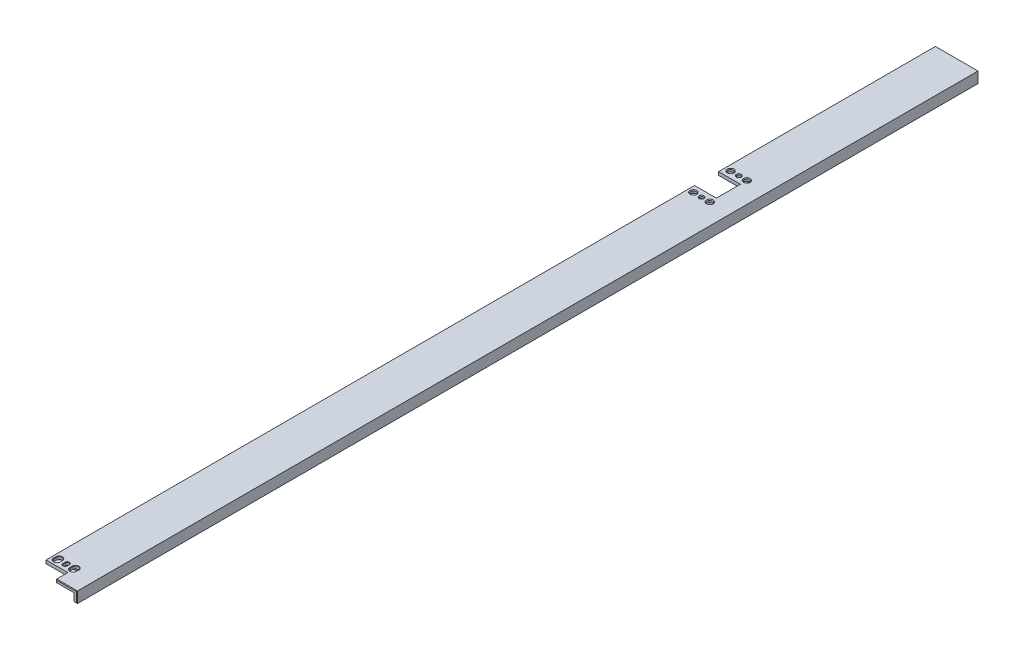
SolidWorks part; units mm, degrees
material "6061 Alloy"
ref_plane "Front" through (0, 0, 0) normal (0, 0, 1) x (1, 0, 0)
ref_plane "Top" through (0, 0, 0) normal (0, 1, 0) x (1, 0, 0)
ref_plane "Right" through (0, 0, 0) normal (1, 0, 0) x (0, 0, -1)
sketch "Sketch1" plane through (0, 0, 0) normal (0, 1, 0) x (1, 0, 0)
  line L0 (0, 0) -> (0, 77.3682) construction
  line L1 (0, 0) -> (-68.6698, 0) construction
  line L2 (-69.1, 0) -> (-69.1, 40) construction
  line L3 (-93.1, 190) -> (-93.1, 840) construction
  line L4 (-126.1, 990) -> (-126.1, 2198) construction
  line L5 (-165.1, 2198) -> (-165.1, 0) construction
  line L6 (-165.1, 2198) -> (-126.1, 2198) construction
  line L7 (-165.1, 0) -> (-69.1, 0) construction
  line L8 (-462.2814, 755.9) -> (800.8337, 755.9) construction
  line L9 (-93.1, 755.6) -> (-145.1, 755.6) construction
  line L10 (-145.1, 755.6) -> (-145.1, 744.9) construction
  line L11 (-145.1, 744.9) -> (-165.1, 744.9) construction
  line L12 (-450.7799, 139.9) -> (404.4044, 139.9) construction
  line L13 (-165.1, 150.9) -> (-145.1, 150.9) construction
  line L14 (-145.1, 150.9) -> (-145.1, 128.9) construction
  line L15 (-145.1, 128.9) -> (-165.1, 128.9) construction
  line L16 (-165.1, 128.9) -> (-165.1, 0) construction
  line L17 (-165.1, 744.9) -> (-165.1, 150.9) construction
  line L18 (-93.1, 755.6) -> (-93.1, 190) construction
  line L19 (-752.0446, 1371.9) -> (535.2926, 1371.9) construction
  line L20 (-878.4617, 1987.9) -> (588.9463, 1987.9) construction
  line L21 (-93.1, 756.2) -> (-145.1, 756.2) construction
  line L22 (-145.1, 756.2) -> (-145.1, 766.9) construction
  line L23 (-145.1, 766.9) -> (-165.1, 766.9) construction
  line L24 (-107.1553, 756.2) -> (-107.1553, 755.6) construction
  line L25 (-144.4764, 1372.2) -> (-144.4764, 1371.6) construction
  line L26 (-126.1, 1371.6) -> (-145.1, 1371.6) construction
  line L27 (-165.1, 1360.9) -> (-165.1, 766.9) construction
  line L28 (-126.1, 1371.6) -> (-126.1, 990) construction
  line L29 (-93.1, 756.2) -> (-93.1, 840) construction
  line L30 (-145.1, 1371.6) -> (-145.1, 1360.9) construction
  line L31 (-145.1, 1360.9) -> (-165.1, 1360.9) construction
  line L32 (-126.1, 2198) -> (-165.1, 2198)
  line L33 (-145.1, 1987.6) -> (-145.1, 1976.9)
  line L34 (-145.1, 1976.9) -> (-165.1, 1976.9)
  line L35 (-165.1, 1382.9) -> (-165.1, 1976.9)
  line L36 (-145.1, 1382.9) -> (-165.1, 1382.9)
  line L37 (-145.1, 1372.2) -> (-145.1, 1382.9)
  line L38 (-126.1, 1372.2) -> (-126.1, 2198)
  line L39 (-126.1, 1372.2) -> (-145.1, 1372.2)
  line L40 (-165.1, 2198) -> (-165.1, 1998.9)
  line L41 (-145.1, 1998.9) -> (-165.1, 1998.9)
  line L42 (-145.1, 1988.2) -> (-145.1, 1998.9)
  line L43 (-145.1, 1987.6) -> (-145.1, 1988.2)
  arc A0 (-93.1, 190) -> (-81.1, 115) centre (147.275, 190) ccw construction
  arc A1 (-81.1, 115) -> (-69.1, 40) centre (-309.475, 40) cw construction
  arc A2 (-126.1, 990) -> (-109.6, 915) centre (52.6045, 990) ccw construction
  arc A3 (-109.6, 915) -> (-93.1, 840) centre (-271.8045, 840) cw construction
  arc A4 (-126.1, 990) -> (-109.6, 915) centre (52.6045, 990) ccw construction
  arc A5 (-109.6, 915) -> (-93.1, 840) centre (-271.8045, 840) cw construction
  point P28 (-145.1, 139.9)
  point P41 (-107.1553, 755.9)
  point P44 (-144.4764, 1371.9)
  dimension "D1" = 2198
  dimension "D2" = 39
  dimension "D3" = 165.1
  dimension "D4" = 24
  dimension "D5" = 33
  dimension "D6" = 40
  dimension "D7" = 150
  dimension "D8" = 840
  dimension "D9" = 150
  dimension "D10" = 755.9
  dimension "D11" = 0.3
  dimension "D12" = 11
  dimension "D13" = 20
  dimension "D14" = 139.9
  dimension "D15" = 22
  dimension "D16" = 616
  dimension "D17" = 616
extrude "Extrude1" add sketch "Sketch1" against normal blind 10
sketch "Sketch4" plane through (0, -10, 0) normal (0, -1, 0) x (1, 0, 0)
  line L0 (-83.1, 0) -> (-83.1, -40) construction
  line L1 (-107.1, -190) -> (-107.1, -190.4) construction
  line L2 (-100.1, -755.6) -> (-107.1, -755.6) construction
  line L3 (-107.1, -755.6) -> (-107.1, -707.4) construction
  line L4 (-145.1, -1372.2) -> (-126.1, -1372.2) construction
  line L5 (-165.1, -2198) -> (-165.1, -1998.9) construction
  line L6 (-76.1, 0) -> (-76.1, -40) construction
  line L7 (-100.1, -190) -> (-100.1, -755.6) construction
  line L8 (-107.1, -707.4) -> (-165.1, -707.4) construction
  line L10 (-165.1, -707.4) -> (-165.1, -190.4) construction
  line L11 (-165.1, -190.4) -> (-107.1, -190.4) construction
  line L13 (-83.1, 0) -> (-76.1, 0) construction
  line L18 (-165.1, -796.9) -> (-106.1, -796.9) construction
  line L21 (-165.1, -1360.9) -> (-165.1, -766.9) construction
  line L24 (-99.1, -756.2) -> (-99.1, -840) construction
  line L25 (-132.1, -990) -> (-132.1, -1371.6) construction
  line L26 (-106.1, -796.9) -> (-106.1, -756.2) construction
  line L27 (-99.1, -756.2) -> (-106.1, -756.2) construction
  line L28 (-93.1, -756.2) -> (-145.1, -756.2) construction
  line L30 (-145.1, -766.9) -> (-165.1, -766.9) construction
  line L31 (-132.1, -1371.6) -> (-139.1, -1371.6) construction
  line L32 (-139.1, -1371.6) -> (-139.1, -1330.9) construction
  line L33 (-139.1, -1330.9) -> (-165.1, -1330.9) construction
  line L34 (-145.1, -1360.9) -> (-165.1, -1360.9) construction
  line L35 (-165.1, -796.9) -> (-165.1, -1330.9) construction
  line L36 (-126.1, -1372.2) -> (-145.1, -1372.2) construction
  line L38 (-139.1, -1372.2) -> (-129.1, -1372.2)
  line L39 (-129.1, -1372.2) -> (-129.1, -2198)
  line L40 (-126.1, -2198) -> (-165.1, -2198) construction
  line L41 (-126.1, -1372.2) -> (-126.1, -2198) construction
  line L42 (-139.1, -1372.2) -> (-139.1, -1412.9)
  line L43 (-139.1, -1412.9) -> (-165.1, -1412.9)
  line L44 (-165.1, -1412.9) -> (-165.1, -1946.9)
  line L45 (-165.1, -1946.9) -> (-139.1, -1946.9)
  line L46 (-139.1, -1946.9) -> (-139.1, -2198)
  line L47 (-139.1, -2198) -> (-129.1, -2198)
  line L48 (-145.1, -1382.9) -> (-165.1, -1382.9) construction
  line L49 (-145.1, -1976.9) -> (-165.1, -1976.9) construction
  line L51 (-165.1, -1382.9) -> (-165.1, -1976.9) construction
  arc A0 (-94.6008, -111.8799) -> (-83.1, -40) centre (-313.475, -40) ccw construction
  arc A1 (-94.6008, -111.8799) -> (-107.1, -190) centre (143.275, -190) ccw construction
  arc A6 (-87.9502, -114.064) -> (-76.1, -40) centre (-313.475, -40) ccw construction
  arc A7 (-87.9502, -114.064) -> (-100.1, -190) centre (143.275, -190) ccw construction
  arc A15 (-115.323, -913.7409) -> (-99.1, -840) centre (-274.8045, -840) ccw construction
  arc A16 (-115.323, -913.7409) -> (-132.1, -990) centre (49.6045, -990) ccw construction
  dimension "D3" = 26
  dimension "D4" = 3
  dimension "D5" = 30
  dimension "D6" = 7
  dimension "D7" = 7
  dimension "D8" = 30
  dimension "D10" = 30
  dimension "D11" = 30
  dimension "D2" = 7
extrude "Extrude2" cut sketch "Sketch4" against normal offset from surface (7 mm away) 3 up to face at (-149.3, 0, -1785.78)
sketch "Sketch5" plane through (0, -10, 0) normal (0, -1, 0) x (1, 0, 0)
  line L0 (-139.1, -1412.9) -> (-139.1, -1372.2) construction
  line L1 (-165.1, -106.4) -> (-139.1, -106.4) construction
  line L2 (-165.1, -106.4) -> (-165.1, -173.4) construction
  line L3 (-165.1, -173.4) -> (-139.1, -173.4) construction
  line L4 (-139.1, -106.4) -> (-139.1, -173.4) construction
  line L5 (-165.1, -1382.9) -> (-139.1, -1382.9)
  line L6 (-165.1, -1382.9) -> (-165.1, -1397.9)
  line L7 (-165.1, -721.4) -> (-139.1, -721.4) construction
  line L8 (-165.1, -721.4) -> (-165.1, -737.4) construction
  line L9 (-165.1, -737.4) -> (-139.1, -737.4) construction
  line L10 (-139.1, -721.4) -> (-139.1, -737.4) construction
  line L12 (-165.1, -774.4) -> (-139.1, -774.4) construction
  line L13 (-165.1, -774.4) -> (-165.1, -790.4) construction
  line L14 (-165.1, -790.4) -> (-139.1, -790.4) construction
  line L15 (-139.1, -774.4) -> (-139.1, -790.4) construction
  line L17 (-165.1, -1353.4) -> (-139.1, -1353.4) construction
  line L18 (-165.1, -1353.4) -> (-165.1, -1338.4) construction
  line L19 (-165.1, -1338.4) -> (-139.1, -1338.4) construction
  line L20 (-139.1, -1353.4) -> (-139.1, -1338.4) construction
  line L21 (-165.1, -1397.9) -> (-139.1, -1397.9)
  line L22 (-139.1, -1382.9) -> (-139.1, -1397.9)
  line L23 (-139.1, -2198) -> (-139.1, -1946.9) construction
  line L24 (-165.1, -1998.9) -> (-139.1, -1998.9)
  line L25 (-165.1, -1998.9) -> (-165.1, -2013.9)
  line L26 (-165.1, -2013.9) -> (-139.1, -2013.9)
  line L27 (-139.1, -1998.9) -> (-139.1, -2013.9)
  line L28 (-139.1, -1946.9) -> (-139.1, -2198) construction
  line L29 (-165.1, -1976.9) -> (-139.1, -1976.9)
  line L30 (-165.1, -1976.9) -> (-165.1, -1961.9)
  line L31 (-165.1, -1961.9) -> (-139.1, -1961.9)
  line L32 (-139.1, -1976.9) -> (-139.1, -1961.9)
  dimension "D1" = 67
  dimension "D2" = 16
  dimension "D3" = 16
  dimension "D4" = 15
  dimension "D5" = 15
  dimension "D6" = 15
extrude "Extrude3" cut sketch "Sketch5" against normal up to surface (7 mm away) up to face at (-143.1, -3, -1732.5)
sketch "Sketch16" plane through (0, -10, 0) normal (0, -1, 0) x (1, 0, 0)
  line L0 (-139.1, -1998.9) -> (-145.1, -1998.9) construction
  line L1 (-145.1, -1998.9) -> (-145.1, -1976.9) construction
  line L2 (-145.1, -1976.9) -> (-139.1, -1976.9) construction
  line L3 (-139.1, -1976.9) -> (-139.1, -1998.9) construction
  line L4 (-139.1, -1998.9) -> (-145.1, -1998.9)
  line L5 (-145.1, -1998.9) -> (-145.1, -1976.9)
  line L6 (-145.1, -1976.9) -> (-139.1, -1976.9)
  line L7 (-139.1, -1976.9) -> (-139.1, -1998.9)
  line L8 (-139.1, -1372.2) -> (-139.1, -1382.9) construction
  line L9 (-145.1, -1372.2) -> (-139.1, -1372.2) construction
  line L10 (-145.1, -1382.9) -> (-145.1, -1372.2) construction
  line L11 (-139.1, -1382.9) -> (-145.1, -1382.9) construction
  line L12 (-139.1, -1372.2) -> (-139.1, -1382.9)
  line L13 (-145.1, -1372.2) -> (-139.1, -1372.2)
  line L14 (-145.1, -1382.9) -> (-145.1, -1372.2)
  line L15 (-139.1, -1382.9) -> (-145.1, -1382.9)
extrude "Extrude8" cut sketch "Sketch16" against normal up to surface (7 mm away) up to face at (-148.0565, -3, -1768.8478)
sketch "Sketch8" plane through (0, -3, 0) normal (0, -1, 0) x (1, 0, 0)
  line L0 (-450.7799, -139.9) -> (404.4044, -139.9) construction
  line L1 (-160.1, -115.4) -> (-145.1, -115.4) construction
  line L2 (-160.1, -115.4) -> (-160.1, -164.4) construction
  line L3 (-160.1, -164.4) -> (-145.1, -164.4) construction
  line L4 (-145.1, -115.4) -> (-145.1, -164.4) construction
  line L5 (-145.1, -1987.6) -> (-145.1, -1976.9) construction
  line L6 (-160.1, -1970.9) -> (-145.1, -1970.9)
  line L7 (-145.1, -755.9) -> (-160.1, -755.9) construction
  line L8 (-145.1, -755.9) -> (-145.1, -731.4) construction
  line L9 (-145.1, -731.4) -> (-160.1, -731.4) construction
  line L10 (-160.1, -755.9) -> (-160.1, -731.4) construction
  line L11 (-160.1, -1970.9) -> (-160.1, -2004.9)
  line L12 (-160.1, -755.9) -> (-145.1, -755.9)
  line L13 (-160.1, -755.9) -> (-160.1, -772.9)
  line L14 (-160.1, -772.9) -> (-145.1, -772.9)
  line L15 (-145.1, -755.9) -> (-145.1, -772.9)
  line L16 (-160.1, -2004.9) -> (-145.1, -2004.9)
  line L17 (-462.2814, -755.9) -> (800.8337, -755.9) construction
  line L18 (-145.1, -756.2) -> (-145.1, -766.9) construction
  line L19 (-752.0446, -1371.9) -> (535.2926, -1371.9) construction
  line L20 (-160.1, -1371.9) -> (-145.1, -1371.9)
  line L21 (-160.1, -1371.9) -> (-160.1, -1354.9)
  line L22 (-160.1, -1354.9) -> (-145.1, -1354.9)
  line L23 (-145.1, -1371.9) -> (-145.1, -1354.9)
  line L24 (-145.1, -1970.9) -> (-145.1, -2004.9)
  line L27 (-878.4617, -1987.9) -> (588.9463, -1987.9) construction
  line L29 (-160.1, -1371.9) -> (-145.1, -1371.9)
  line L30 (-160.1, -1371.9) -> (-160.1, -1388.9)
  line L31 (-160.1, -1388.9) -> (-145.1, -1388.9)
  line L32 (-145.1, -1371.9) -> (-145.1, -1388.9)
  point P4 (-160.1, -139.9)
  point P9 (-152.6, -115.4)
  point P10 (-152.6, -164.4)
  point P17 (-152.6, -731.4)
  point P23 (-152.6, -772.9)
  point P28 (-152.6, -1354.9)
  point P35 (-160.1, -1987.9)
  point P38 (-152.6, -2004.9)
  point P41 (-152.6, -1388.9)
  point P42 (-152.6, -1970.9)
  dimension "D1" = 15
  dimension "D2" = 15
  dimension "D3" = 49
  dimension "D4" = 24.5
  dimension "D5" = 17
  dimension "D6" = 15
  dimension "D7" = 0
  dimension "D8" = 0
  dimension "D9" = 34
hole_wizard "1/8 (0.125) Diameter Hole1" positions "3DSketch1" profile "Sketch9" hole size "1/8" standard "Ansi Inch" end condition through all
sketch3d "3DSketch1"
  point P0 (-152.6, -3, -2004.9)
sketch "Sketch9" plane through (-152.6, -3, -2004.9) normal (1, 0, 0) x (0, 0, -1)
  line L0 (0, 0) -> (0, 3)
  line L1 (0, 3) -> (2.2479, 3)
  line L2 (1.6129, 2.365) -> (1.6129, 0.635)
  line L3 (1.6129, 0.635) -> (2.2479, 0)
  line L5 (2.2479, 0) -> (0, 0)
  line L6 (-1.6129, 0.635) -> (-2.2479, 0) construction
  line L7 (2.2479, 3) -> (1.6129, 2.365)
  line L8 (-2.2479, 3) -> (-1.6129, 2.365) construction
  line L11 (0, -6.35) -> (0, 107.95) construction
  dimension "Thru Hole Dia." = 3.2258
  dimension "Thru Hole Depth" = 3
  dimension "Near C'Sink Dia." = 4.4958
  dimension "Near C'Sink Angle" = 90
  dimension "Far C'Sink Dia." = 4.4958
  dimension "Far C'Sink Angle" = 90
hole_wizard "1/8 (0.125) Diameter Hole2" positions "3DSketch5" profile "Sketch17" hole size "1/8" standard "Ansi Inch" end condition up to next
sketch3d "3DSketch5"
  point P0 (-152.6, -3, -1970.9)
sketch "Sketch17" plane through (-152.6, -3, -1970.9) normal (1, 0, 0) x (0, 0, -1)
  line L0 (0, 0) -> (0, 3)
  line L1 (0, 3) -> (2.2479, 3)
  line L2 (1.6129, 2.365) -> (1.6129, 0.635)
  line L3 (1.6129, 0.635) -> (2.2479, 0)
  line L5 (2.2479, 0) -> (0, 0)
  line L6 (-1.6129, 0.635) -> (-2.2479, 0) construction
  line L7 (2.2479, 3) -> (1.6129, 2.365)
  line L8 (-2.2479, 3) -> (-1.6129, 2.365) construction
  line L11 (0, -6.35) -> (0, 107.95) construction
  dimension "Thru Hole Dia." = 3.2258
  dimension "Thru Hole Depth" = 3
  dimension "Near C'Sink Dia." = 4.4958
  dimension "Near C'Sink Angle" = 90
  dimension "Far C'Sink Dia." = 4.4958
  dimension "Far C'Sink Angle" = 90
hole_wizard "#8 Clearance Hole1" positions "3DSketch2" profile "Sketch10" hole size "#8" standard "Ansi Inch" end condition through all
sketch3d "3DSketch2"
  point P0 (-160.1, -3, -1970.9)
  point P3 (-145.1, -3, -1970.9)
sketch "Sketch10" plane through (-160.1, -3, -1970.9) normal (1, 0, 0) x (0, 0, -1)
  line L0 (0, 0) -> (0, 3)
  line L1 (0, 3) -> (3.0861, 3)
  line L2 (2.4574, 2.3714) -> (2.4574, 0.635)
  line L3 (2.4574, 0.635) -> (3.0924, 0)
  line L5 (3.0924, 0) -> (0, 0)
  line L6 (-2.4574, 0.635) -> (-3.0924, 0) construction
  line L7 (3.0861, 3) -> (2.4574, 2.3714)
  line L8 (-3.0861, 3) -> (-2.4575, 2.3713) construction
  line L11 (0, -6.35) -> (0, 107.95) construction
  dimension "Thru Hole Dia." = 4.9149
  dimension "Thru Hole Depth" = 3
  dimension "Near C'Sink Dia." = 6.1849
  dimension "Near C'Sink Angle" = 90
  dimension "Far C'Sink Dia." = 6.1722
  dimension "Far C'Sink Angle" = 90
hole_wizard "#8 Clearance Hole2" positions "3DSketch4" profile "Sketch14" hole size "#8" standard "Ansi Inch" end condition through all
sketch3d "3DSketch4"
  point P0 (-160.1, -3, -2004.9)
  point P3 (-145.1, -3, -2004.9)
sketch "Sketch14" plane through (-160.1, -3, -2004.9) normal (1, 0, 0) x (0, 0, -1)
  line L0 (0, 0) -> (0, 3)
  line L1 (0, 3) -> (3.0861, 3)
  line L2 (2.4574, 2.3713) -> (2.4574, 0.635)
  line L3 (2.4574, 0.635) -> (3.0924, 0)
  line L5 (3.0924, 0) -> (0, 0)
  line L6 (-2.4574, 0.635) -> (-3.0924, 0) construction
  line L7 (3.0861, 3) -> (2.4574, 2.3713)
  line L8 (-3.0861, 3) -> (-2.4574, 2.3713) construction
  line L11 (0, -6.35) -> (0, 107.95) construction
  dimension "Thru Hole Dia." = 4.9149
  dimension "Thru Hole Depth" = 3
  dimension "Near C'Sink Dia." = 6.1849
  dimension "Near C'Sink Angle" = 90
  dimension "Far C'Sink Dia." = 6.1722
  dimension "Far C'Sink Angle" = 90
sketch "Sketch12" plane through (0, -3, 0) normal (0, -1, 0) x (1, 0, 0)
  line L0 (-152.6, -730.4) -> (-152.6, -732.4) construction
  line L1 (-154.251, -730.4) -> (-150.949, -730.4) construction
  line L2 (-154.251, -730.4) -> (-154.251, -732.4) construction
  line L3 (-154.251, -732.4) -> (-150.949, -732.4) construction
  line L4 (-150.949, -730.4) -> (-150.949, -732.4) construction
  line L5 (-152.6, -1387.9) -> (-152.6, -1389.9) construction
  line L6 (-154.251, -1387.9) -> (-150.949, -1387.9) construction
  line L7 (-154.251, -1387.9) -> (-154.251, -1389.9)
  line L8 (-154.251, -1389.9) -> (-150.949, -1389.9) construction
  line L9 (-150.949, -1387.9) -> (-150.949, -1389.9)
  line L10 (-145.1, -731.4) -> (-160.1, -731.4) construction
  line L11 (-160.1, -1389.9) -> (-160.1, -1387.9) construction
  line L12 (-162.85, -1389.9) -> (-162.85, -1387.9)
  line L13 (-157.35, -1389.9) -> (-157.35, -1387.9)
  line L14 (-145.1, -1389.9) -> (-145.1, -1387.9) construction
  line L15 (-147.85, -1389.9) -> (-147.85, -1387.9)
  line L16 (-142.35, -1389.9) -> (-142.35, -1387.9)
  arc A0 (-150.949, -730.4) -> (-154.251, -730.4) centre (-152.6, -730.4) ccw construction
  arc A1 (-154.251, -732.4) -> (-150.949, -732.4) centre (-152.6, -732.4) ccw construction
  arc A2 (-150.949, -1387.9) -> (-154.251, -1387.9) centre (-152.6, -1387.9) ccw
  arc A3 (-154.251, -1389.9) -> (-150.949, -1389.9) centre (-152.6, -1389.9) ccw
  arc A4 (-162.85, -1389.9) -> (-157.35, -1389.9) centre (-160.1, -1389.9) ccw
  arc A5 (-157.35, -1387.9) -> (-162.85, -1387.9) centre (-160.1, -1387.9) ccw
  arc A6 (-147.85, -1387.9) -> (-142.35, -1387.9) centre (-145.1, -1387.9) cw
  arc A7 (-142.35, -1389.9) -> (-147.85, -1389.9) centre (-145.1, -1389.9) cw
  point P7 (-152.6, -1388.9)
  point P19 (-152.6, -731.4)
  point P20 (-152.6, -731.4)
  dimension "D5" = 5.5
  dimension "D1" = 3.302
  dimension "D2" = 2
  dimension "D3" = 3.302
  dimension "D4" = 2
  dimension "D6" = 7.5
extrude "Extrude6" cut sketch "Sketch12" against normal through all
sketch "Sketch15" plane through (0, -10, 0) normal (0, -1, 0) x (1, 0, 0)
  line L12 (-146.1, -2191) -> (-146.1, -2020.9)
  line L13 (-146.1, -2020.9) -> (-158.1, -2020.9)
  line L14 (-158.1, -2020.9) -> (-158.1, -2191)
  line L15 (-158.1, -2191) -> (-146.1, -2191)
  line L16 (-146.1, -2191) -> (-146.1, -2020.9)
  line L17 (-146.1, -2020.9) -> (-158.1, -2020.9)
  line L18 (-158.1, -2020.9) -> (-158.1, -2191)
  line L19 (-158.1, -2191) -> (-146.1, -2191)
  dimension "D1" = 7
extrude "Extrude7" cut sketch "Sketch15" against normal up to surface (7 mm away) up to face at (-145.1, -3, -1388.9)
fillet "Fillet1" radius 3.175 4 edges at (-146.1, -6.5, -2191) (-158.1, -6.5, -2191) (-158.1, -6.5, -2020.9) (-146.1, -6.5, -2020.9)
chamfer "Chamfer1" distance 0.5 angle 45 13 edges at (-129.1, -6.5, -2198) (-126.1, -5, -2198) (-139.1, -6.5, -2198) (-134.1, -3, -2198) (-145.6, 0, -2198) (-165.1, -5, -2198) (-152.1, -10, -2198) (-145.1, -1.5, -1372.2) (-137.1, -3, -1372.2) (-135.6, 0, -1372.2) (-126.1, -5, -1372.2) (-127.6, -10, -1372.2) (-129.1, -6.5, -1372.2)
chamfer "Chamfer2" distance 0.3 angle 45 24 edges at (-152.6, -3, -1386.249) (-154.251, -3, -1388.9) (-152.6, -3, -1391.551) (-150.949, -3, -1388.9) (-152.6, 0, -1391.551) (-150.949, 0, -1388.9) (-152.6, 0, -1386.249) (-154.251, 0, -1388.9) (-147.85, -3, -1388.9) (-145.1, -3, -1392.65) (-142.35, -3, -1388.9) (-145.1, -3, -1385.15) (-157.35, -3, -1388.9) (-160.1, -3, -1392.65) (-162.85, -3, -1388.9) (-160.1, -3, -1385.15) (-157.35, 0, -1388.9) (-160.1, 0, -1392.65) (-162.85, 0, -1388.9) (-160.1, 0, -1385.15) (-147.85, 0, -1388.9) (-145.1, 0, -1392.65) (-142.35, 0, -1388.9) (-145.1, 0, -1385.15)
fillet "Fillet4" radius 3 5 edges at (-139.1, -6.5, -2013.9) (-139.1, -6.5, -1961.9) (-139.1, -6.5, -1946.9) (-139.1, -6.5, -1412.9) (-139.1, -6.5, -1397.9)
fillet "Fillet3" radius 0.5 22 edges at (-139.1, -3, -2107.2) (-153.6, -3, -1946.9) (-153.6, -3, -1961.9) (-157.1701, -3, -2190.0701) (-158.1, -3, -2105.95) (-157.1701, -3, -2021.8299) (-152.1, -3, -2020.9) (-147.0299, -3, -2021.8299) (-146.1, -3, -2105.95) (-147.0299, -3, -2190.0701) (-152.1, -3, -2191) (-153.6, -3, -2013.9) (-153.6, -3, -1412.9) (-153.6, -3, -1397.9) (-129.1, -3, -1785.1) (-139.1, -3, -1405.4) (-139.9787, -3, -1947.7787) (-139.1, -3, -1954.4) (-139.9787, -3, -1961.0213) (-139.9787, -3, -2014.7787) (-139.9787, -3, -1412.0213) (-139.9787, -3, -1398.7787)
